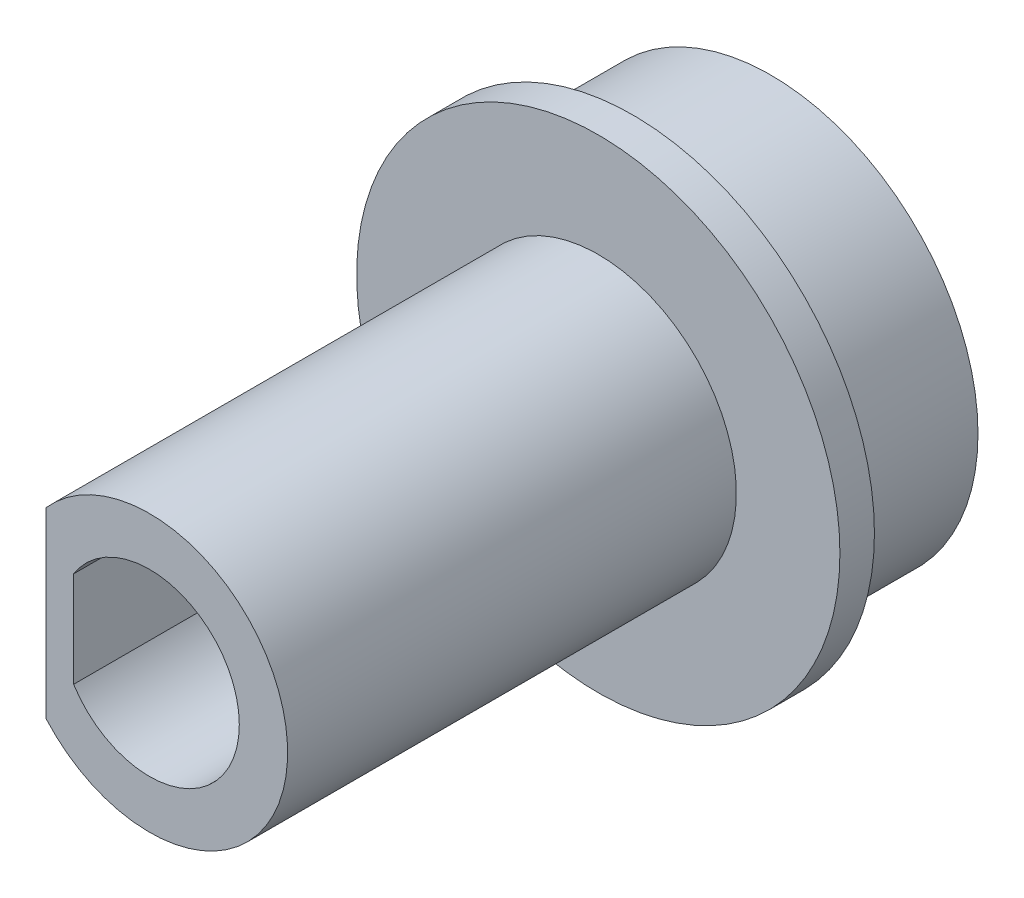
SolidWorks part; units mm, degrees
ref_plane "前视基准面" through (0, 0, 0) normal (0, 0, 1) x (1, 0, 0)
ref_plane "上视基准面" through (0, 0, 0) normal (0, 1, 0) x (1, 0, 0)
ref_plane "右视基准面" through (0, 0, 0) normal (1, 0, 0) x (0, 0, -1)
sketch "草图1" plane through (0, 0, 0) normal (0, 0, 1) x (1, 0, 0)
  circle A0 centre (0, 0) radius 6
  dimension "D1" = 12
extrude "凸台-拉伸1" add sketch "草图1" along normal blind 5
sketch "草图7" plane through (0, 0, 5) normal (0, 0, 1) x (1, 0, 0)
  circle A0 centre (0, 0) radius 7
  dimension "D1" = 14
extrude "凸台-拉伸6" add sketch "草图7" against normal blind 1
sketch "草图2" plane through (0, 0, 5) normal (0, 0, 1) x (1, 0, 0)
  line L0 (-3, 2.6458) -> (-3, -2.6458)
  circle A1 centre (0, 0) radius 4
  dimension "D2" = 8
  dimension "D1" = 3
extrude "凸台-拉伸2" add sketch "草图2" along normal blind 13 contours L0 A1
sketch "草图4" plane through (0, 0, 0) normal (0, 0, -1) x (-1, 0, 0)
  line L0 (-2.6458, -3) -> (2.6458, -3)
  circle A0 centre (0, 0) radius 4
  dimension "D1" = 8
  dimension "D2" = 3
extrude "凸台-拉伸3" [suppressed] add sketch "草图4" along normal blind 15 contours L0 A0
sketch "草图8" plane through (0, 0, 0) normal (0, 0, 1) x (1, 0, 0)
  line L0 (-2.2, 1.3856) -> (-2.2, -1.3856)
  circle A0 centre (0, 0) radius 2.6
  dimension "D1" = 5.2
  dimension "D2" = 2.2
extrude "切除-拉伸1" cut sketch "草图8" along normal through all contours A0 L0
